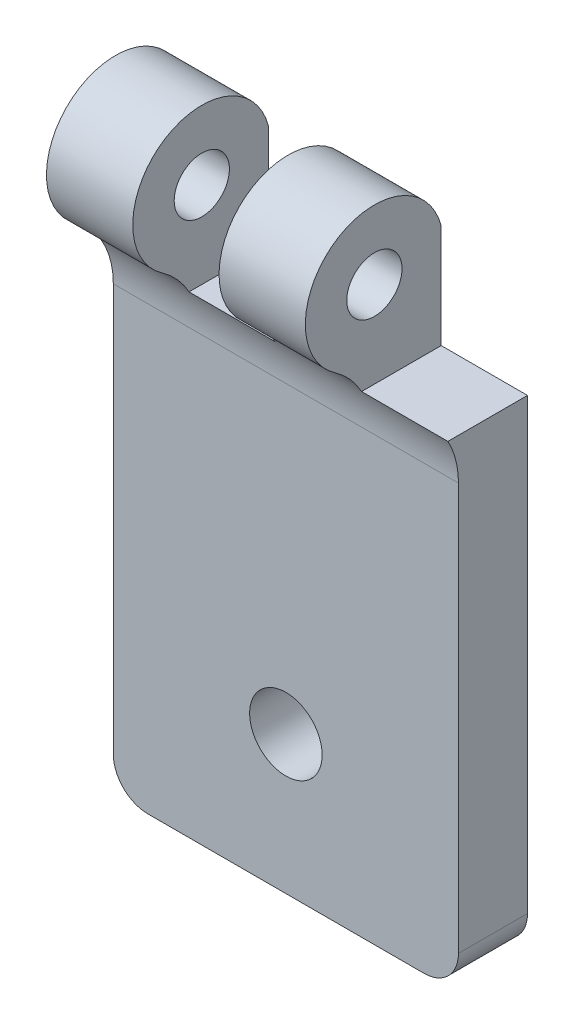
SolidWorks part; units mm, degrees
ref_plane "Front Plane" through (0, 0, 0) normal (0, 0, 1) x (1, 0, 0)
ref_plane "Top Plane" through (0, 0, 0) normal (0, 1, 0) x (1, 0, 0)
ref_plane "Right Plane" through (0, 0, 0) normal (1, 0, 0) x (0, 0, -1)
sketch "Sketch1" plane through (0, 0, 0) normal (0, 0, 1) x (1, 0, 0)
  line L1 (0, 0) -> (-20, 0)
  line L2 (0, 0) -> (0, 34)
  line L3 (0, 34) -> (-20, 34)
  line L4 (-20, 0) -> (-20, 34)
  dimension "D1" = 20
  dimension "D2" = 34
extrude "Boss-Extrude1" add sketch "Sketch1" along normal blind 4
sketch "Sketch2" plane through (0, 0, 0) normal (1, 0, 0) x (0, 0, -1)
  line L0 (-4, 0) -> (-4, 34) construction
  line L1 (-4, 29) -> (-4, 34)
  line L2 (-4, 34) -> (0, 34)
  arc A0 (0, 34) -> (-4, 29) centre (-3.8725, 32.998) ccw
  dimension "D2" = 4
  dimension "D1" = 5
extrude "Boss-Extrude2" add sketch "Sketch2" against normal up to surface (20 mm away) up to face at (-20, 17, 2)
fillet "Fillet1" radius 5 1 edges at (-10, 29, 4)
sketch "Sketch3" plane through (0, 0, 0) normal (1, 0, 0) x (0, 0, -1)
  circle A0 centre (-3.8725, 32.998) radius 1.6
  arc A1 (0, 34) -> (-6.1514, 29.7106) centre (-3.8725, 32.998) ccw construction
  dimension "D1" = 3.2
extrude "Cut-Extrude1" cut sketch "Sketch3" against normal through all
sketch "Sketch4" plane through (0, 0, 4) normal (0, 0, 1) x (1, 0, 0)
  line L0 (0, 0) -> (0, 25.6015) construction
  line L1 (-20, 0) -> (0, 0) construction
  circle A0 centre (-10, 8) radius 2.1
  dimension "D1" = 4.2
  dimension "D2" = 10
  dimension "D3" = 8
extrude "Cut-Extrude2" cut sketch "Sketch4" against normal through all
fillet "Fillet2" radius 2 2 edges at (0, 0, 2) (-20, 0, 2)
sketch "Sketch5" plane through (0, 0, 0) normal (0, 0, -1) x (-1, 0, 0)
  line L0 (0, 2) -> (0, 34) construction
  line L1 (0, 28) -> (5, 28)
  line L2 (0, 28) -> (0, 40)
  line L3 (0, 40) -> (5, 40)
  line L4 (5, 28) -> (5, 40)
  line L5 (18, 0) -> (2, 0) construction
  line L6 (10, 28) -> (15, 28)
  line L7 (10, 28) -> (10, 40)
  line L8 (10, 40) -> (15, 40)
  line L9 (15, 28) -> (15, 40)
  dimension "D1" = 5
  dimension "D2" = 5
  dimension "D3" = 5
  dimension "D4" = 28
  dimension "D5" = 28
  dimension "D6" = 12
  dimension "D7" = 12
extrude "Cut-Extrude3" cut sketch "Sketch5" against normal through all
